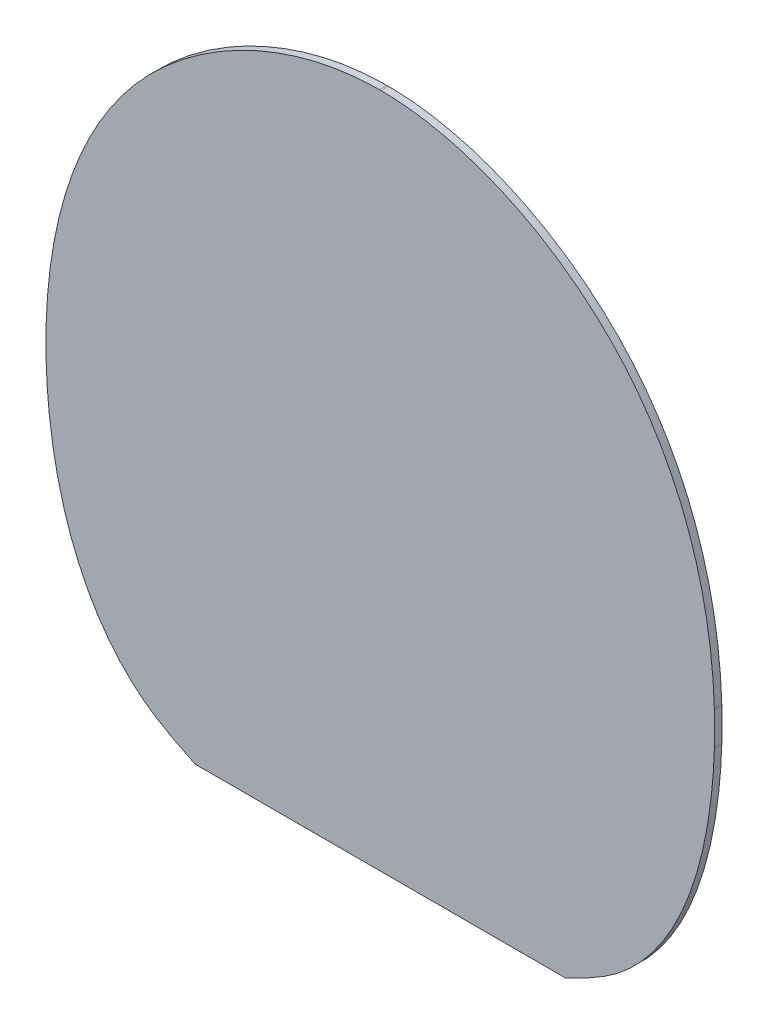
SolidWorks part; units mm, degrees
ref_plane "Front Plane" through (0, 0, 0) normal (0, 0, 1) x (1, 0, 0)
ref_plane "Top Plane" through (0, 0, 0) normal (0, 1, 0) x (1, 0, 0)
ref_plane "Right Plane" through (0, 0, 0) normal (1, 0, 0) x (0, 0, -1)
sketch "Sketch1" plane through (0, 0, 0) normal (0, 0, 1) x (1, 0, 0)
  line L0 (-24.1848, 127.6242) -> (160.1779, 127.6242) construction
  line L1 (90, 300) -> (90, 0) construction
  line L2 (0, 0) -> (180, 0)
  line L3 (0, 0) -> (0, 300)
  line L4 (0, 300) -> (180, 300)
  line L5 (180, 0) -> (180, 300)
  line L6 (72.3747, 0) -> (72.3747, 86.9999)
  line L7 (107.6253, 0) -> (107.6253, 86.9999)
  line L8 (40.101, 117.8404) -> (139.899, 117.8404)
  spline S0 degree 3 poles (72.3747, 86.9999) (71.9459, 95.9781) (52.5134, 113.8663) (31.1047, 121.0691) (7.1517, 142.8938) (-6.8857, 200.2363) (13.8242, 274.6667) (66.9865, 300.0409) (90, 300) knots 0 0 0 0 0.116861 0.211663 0.246387 0.4641 0.758219 1 1 1 1
  spline S1 degree 3 poles (107.6253, 86.9999) (108.0541, 95.9781) (127.4866, 113.8663) (148.8953, 121.0691) (172.8483, 142.8938) (186.8857, 200.2363) (166.1758, 274.6667) (113.0135, 300.0409) (90, 300) knots 0 0 0 0 0.116861 0.211663 0.246387 0.4641 0.758219 1 1 1 1
  dimension "D1" = 300
  dimension "D2" = 180
extrude "Boss-Extrude2" add sketch "Sketch1" along normal blind 2 contours L7 S1 L5 L4 S0 L3 L6 L2
